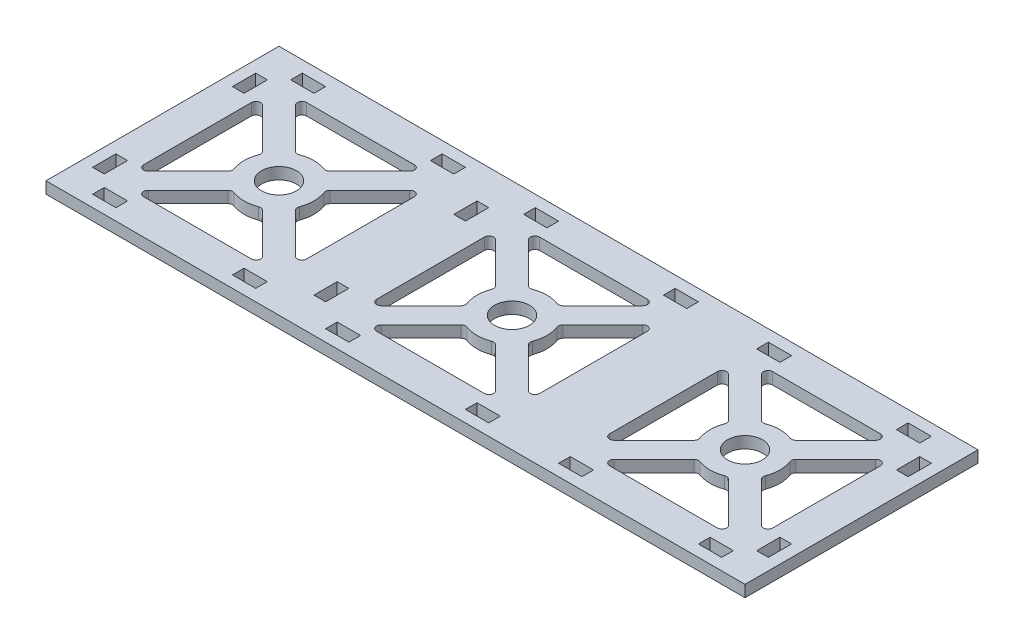
SolidWorks part; units mm, degrees
ref_plane "Front Plane" through (0, 0, 0) normal (0, 0, 1) x (1, 0, 0)
ref_plane "Top Plane" through (0, 0, 0) normal (0, 1, 0) x (1, 0, 0)
ref_plane "Right Plane" through (0, 0, 0) normal (1, 0, 0) x (0, 0, -1)
sketch "Sketch1" plane through (0, 0, 0) normal (0, 1, 0) x (1, 0, 0)
  line L0 (-966.8368, 0) -> (47375.0043, 0) construction
  line L1 (-23.1005, 35) -> (23.1005, 35)
  line L2 (-35, 23.1005) -> (-35, -23.1005)
  line L3 (-23.1005, -35) -> (23.1005, -35)
  line L4 (35, 23.1005) -> (35, -23.1005)
  line L5 (-35, 35) -> (35, -35) construction
  line L6 (-35, -35) -> (35, 35) construction
  line L7 (-50, 50) -> (150, 50)
  line L8 (-50, 50) -> (-50, -50) construction
  line L9 (-50, -50) -> (150, -50)
  line L10 (50, 50) -> (50, -50) construction
  line L11 (-50, 50) -> (50, -50) construction
  line L12 (-50, -50) -> (50, 50) construction
  line L13 (-31.5858, 24.5147) -> (-14.49, 7.4189)
  line L14 (-24.5147, 31.5858) -> (-7.4189, 14.49)
  line L15 (0, -1000) -> (0, 49000) construction
  line L16 (24.5147, 31.5858) -> (7.4189, 14.49)
  line L17 (31.5858, 24.5147) -> (14.49, 7.4189)
  line L18 (31.5858, -24.5147) -> (14.49, -7.4189)
  line L19 (24.5147, -31.5858) -> (7.4189, -14.49)
  line L20 (-24.5147, -31.5858) -> (-7.4189, -14.49)
  line L21 (-31.5858, -24.5147) -> (-14.49, -7.4189)
  line L22 (-35, 35) -> (-35, 27.9289) construction
  line L23 (-23.8844, 35) -> (-27.9289, 35) construction
  line L24 (27.9289, 35) -> (35, 35) construction
  line L25 (35, 35) -> (35, 27.9289) construction
  line L26 (35, -27.9289) -> (35, -35) construction
  line L27 (27.9289, -35) -> (35, -35) construction
  line L28 (-35, -35) -> (-27.9289, -35) construction
  line L29 (-35, -27.9289) -> (-35, -35) construction
  line L30 (135, -27.9289) -> (135, -35) construction
  line L31 (135, -35) -> (127.9289, -35) construction
  line L32 (72.0711, -35) -> (65, -35) construction
  line L33 (65, -27.9289) -> (65, -35) construction
  line L34 (65, 35) -> (65, 27.9289) construction
  line L35 (72.0711, 35) -> (65, 35) construction
  line L36 (123.8844, 35) -> (127.9289, 35) construction
  line L37 (135, 35) -> (135, 27.9289) construction
  line L38 (100, -1000) -> (100, 49000) construction
  line L39 (150, -50) -> (50, 50) construction
  line L40 (150, 50) -> (50, -50) construction
  line L41 (135, -35) -> (65, 35) construction
  line L42 (135, 35) -> (65, -35) construction
  line L43 (1066.8368, 0) -> (-47275.0043, 0) construction
  line L44 (131.5858, -24.5147) -> (114.49, -7.4189)
  line L45 (124.5147, -31.5858) -> (107.4189, -14.49)
  line L46 (75.4853, -31.5858) -> (92.5811, -14.49)
  line L47 (68.4142, -24.5147) -> (85.51, -7.4189)
  line L48 (68.4142, 24.5147) -> (85.51, 7.4189)
  line L49 (75.4853, 31.5858) -> (92.5811, 14.49)
  line L50 (124.5147, 31.5858) -> (107.4189, 14.49)
  line L51 (131.5858, 24.5147) -> (114.49, 7.4189)
  line L52 (150, 50) -> (150, -50)
  line L53 (65, 23.1005) -> (65, -23.1005)
  line L54 (123.1005, -35) -> (76.8995, -35)
  line L55 (135, 23.1005) -> (135, -23.1005)
  line L56 (123.1005, 35) -> (76.8995, 35)
  line L57 (-1166.8368, 0) -> (47175.0043, 0) construction
  line L58 (-65, -27.9289) -> (-65, -35) construction
  line L59 (-65, -35) -> (-72.0711, -35) construction
  line L60 (-127.9289, -35) -> (-135, -35) construction
  line L61 (-135, -27.9289) -> (-135, -35) construction
  line L62 (-135, 35) -> (-135, 27.9289) construction
  line L63 (-127.9289, 35) -> (-135, 35) construction
  line L64 (-76.1156, 35) -> (-72.0711, 35) construction
  line L65 (-65, 35) -> (-65, 27.9289) construction
  line L66 (-100, -1000) -> (-100, 49000) construction
  line L67 (-50, -50) -> (-150, 50) construction
  line L68 (-50, 50) -> (-150, -50) construction
  line L69 (-65, -35) -> (-135, 35) construction
  line L70 (-65, 35) -> (-135, -35) construction
  line L71 (866.8368, 0) -> (-47475.0043, 0) construction
  line L72 (-68.4142, -24.5147) -> (-85.51, -7.4189)
  line L73 (-75.4853, -31.5858) -> (-92.5811, -14.49)
  line L74 (-124.5147, -31.5858) -> (-107.4189, -14.49)
  line L75 (-131.5858, -24.5147) -> (-114.49, -7.4189)
  line L76 (-131.5858, 24.5147) -> (-114.49, 7.4189)
  line L77 (-124.5147, 31.5858) -> (-107.4189, 14.49)
  line L78 (-75.4853, 31.5858) -> (-92.5811, 14.49)
  line L79 (-68.4142, 24.5147) -> (-85.51, 7.4189)
  line L80 (-50, -50) -> (-150, -50)
  line L81 (-50, 50) -> (-150, 50)
  line L82 (-135, 23.1005) -> (-135, -23.1005)
  line L83 (-76.8995, -35) -> (-123.1005, -35)
  line L84 (-65, 23.1005) -> (-65, -23.1005)
  line L85 (-76.8995, 35) -> (-123.1005, 35)
  line L86 (-150, 50) -> (-150, -50)
  line L87 (-65, 40) -> (-75, 40)
  line L88 (-145, 45) -> (145, 45) construction
  line L89 (-145, 45) -> (-145, -45) construction
  line L90 (-145, -45) -> (145, -45) construction
  line L91 (145, 45) -> (145, -45) construction
  line L92 (-145, 45) -> (145, -45) construction
  line L93 (-145, -45) -> (145, 45) construction
  line L98 (-135, 45) -> (-125, 45)
  line L99 (-135, 45) -> (-135, 40)
  line L100 (-135, 40) -> (-125, 40)
  line L101 (-125, 45) -> (-125, 40)
  line L102 (-75, 45) -> (-75, 40)
  line L103 (-65, 45) -> (-75, 45)
  line L104 (-65, 45) -> (-65, 40)
  line L105 (-35, 45) -> (-35, 40)
  line L106 (-35, 40) -> (-25, 40)
  line L107 (-35, 45) -> (-25, 45)
  line L108 (-25, 45) -> (-25, 40)
  line L109 (125, 45) -> (125, 40)
  line L110 (135, 40) -> (125, 40)
  line L111 (135, 45) -> (135, 40)
  line L112 (135, 45) -> (125, 45)
  line L113 (25, 45) -> (25, 40)
  line L114 (35, 45) -> (25, 45)
  line L115 (35, 40) -> (25, 40)
  line L116 (35, 45) -> (35, 40)
  line L117 (65, 45) -> (65, 40)
  line L118 (65, 45) -> (75, 45)
  line L119 (75, 45) -> (75, 40)
  line L120 (65, 40) -> (75, 40)
  line L121 (135, -45) -> (125, -45)
  line L122 (135, -45) -> (135, -40)
  line L123 (135, -40) -> (125, -40)
  line L124 (125, -45) -> (125, -40)
  line L125 (65, -40) -> (75, -40)
  line L126 (75, -45) -> (75, -40)
  line L127 (65, -45) -> (75, -45)
  line L128 (65, -45) -> (65, -40)
  line L129 (35, -45) -> (35, -40)
  line L130 (35, -40) -> (25, -40)
  line L131 (35, -45) -> (25, -45)
  line L132 (25, -45) -> (25, -40)
  line L133 (-125, -45) -> (-125, -40)
  line L134 (-135, -40) -> (-125, -40)
  line L135 (-135, -45) -> (-135, -40)
  line L136 (-135, -45) -> (-125, -45)
  line L137 (-65, -45) -> (-65, -40)
  line L138 (-65, -45) -> (-75, -45)
  line L139 (-75, -45) -> (-75, -40)
  line L140 (-65, -40) -> (-75, -40)
  line L141 (-25, -45) -> (-25, -40)
  line L142 (-35, -45) -> (-25, -45)
  line L143 (-35, -40) -> (-25, -40)
  line L144 (-35, -45) -> (-35, -40)
  line L145 (-140, -35) -> (-140, -25)
  line L146 (-145, 35) -> (-140, 35)
  line L147 (-145, 35) -> (-145, 25)
  line L148 (-145, 25) -> (-140, 25)
  line L149 (-140, 35) -> (-140, 25)
  line L150 (-145, -25) -> (-140, -25)
  line L151 (-145, -35) -> (-145, -25)
  line L152 (-145, -35) -> (-140, -35)
  line L153 (145, -35) -> (140, -35)
  line L154 (145, -35) -> (145, -25)
  line L155 (145, -25) -> (140, -25)
  line L156 (140, -35) -> (140, -25)
  line L157 (140, 35) -> (140, 25)
  line L158 (145, 25) -> (140, 25)
  line L159 (145, 35) -> (145, 25)
  line L160 (145, 35) -> (140, 35)
  line L161 (-50, 35) -> (-50, 25)
  line L162 (-50, 35) -> (-45, 35)
  line L163 (-50, -35) -> (-45, -35)
  line L164 (-50, -25) -> (-45, -25)
  line L165 (-50, 25) -> (-45, 25)
  line L166 (-50, -35) -> (-50, -25)
  line L167 (-45, 35) -> (-45, 25)
  line L168 (-45, -35) -> (-45, -25)
  circle A0 centre (0, 0) radius 7.5
  arc A1 (-5.2983, -14.0331) -> (5.2983, -14.0331) centre (0, 0) ccw
  arc A2 (-13.5355, -6.4645) -> (-10.6066, -10.6066) centre (0, 0) ccw construction
  arc A3 (-10.6066, -10.6066) -> (-6.4645, -13.5355) centre (0, 0) ccw construction
  arc A4 (-10.6066, 10.6066) -> (-13.5355, 6.4645) centre (0, 0) ccw construction
  arc A5 (-14.0331, 5.2983) -> (-14.0331, -5.2983) centre (0, 0) ccw
  arc A6 (-6.4645, 13.5355) -> (-10.6066, 10.6066) centre (0, 0) ccw construction
  arc A7 (10.6066, 10.6066) -> (6.4645, 13.5355) centre (0, 0) ccw construction
  arc A8 (5.2983, 14.0331) -> (-5.2983, 14.0331) centre (0, 0) ccw
  arc A9 (13.5355, 6.4645) -> (10.6066, 10.6066) centre (0, 0) ccw construction
  arc A10 (10.6066, -10.6066) -> (13.5355, -6.4645) centre (0, 0) ccw construction
  arc A11 (14.0331, -5.2983) -> (14.0331, 5.2983) centre (0, 0) ccw
  arc A12 (6.4645, -13.5355) -> (10.6066, -10.6066) centre (0, 0) ccw construction
  arc A13 (-14.0331, 5.2983) -> (-14.49, 7.4189) centre (-15.9042, 6.0047) ccw
  arc A14 (-14.0331, -5.2983) -> (-14.49, -7.4189) centre (-15.9042, -6.0047) cw
  arc A15 (-31.5858, -24.5147) -> (-35, -23.1005) centre (-33, -23.1005) cw
  arc A16 (-31.5858, 24.5147) -> (-35, 23.1005) centre (-33, 23.1005) ccw
  arc A17 (-23.1005, -35) -> (-24.5147, -31.5858) centre (-23.1005, -33) cw
  arc A18 (23.1005, -35) -> (24.5147, -31.5858) centre (23.1005, -33) ccw
  arc A19 (7.4189, -14.49) -> (5.2983, -14.0331) centre (6.0047, -15.9042) ccw
  arc A20 (-5.2983, -14.0331) -> (-7.4189, -14.49) centre (-6.0047, -15.9042) ccw
  arc A21 (35, 23.1005) -> (31.5858, 24.5147) centre (33, 23.1005) ccw
  arc A22 (35, -23.1005) -> (31.5858, -24.5147) centre (33, -23.1005) cw
  arc A23 (14.49, -7.4189) -> (14.0331, -5.2983) centre (15.9042, -6.0047) cw
  arc A24 (14.0331, 5.2983) -> (14.49, 7.4189) centre (15.9042, 6.0047) cw
  arc A25 (7.4189, 14.49) -> (5.2983, 14.0331) centre (6.0047, 15.9042) cw
  arc A26 (-5.2983, 14.0331) -> (-7.4189, 14.49) centre (-6.0047, 15.9042) cw
  arc A27 (23.1005, 35) -> (24.5147, 31.5858) centre (23.1005, 33) cw
  arc A28 (-23.1005, 35) -> (-24.5147, 31.5858) centre (-23.1005, 33) ccw
  arc A29 (93.5355, -13.5355) -> (89.3934, -10.6066) centre (100, 0) cw construction
  arc A30 (89.3934, -10.6066) -> (86.4645, -6.4645) centre (100, 0) cw construction
  arc A31 (86.4645, 6.4645) -> (89.3934, 10.6066) centre (100, 0) cw construction
  arc A32 (89.3934, 10.6066) -> (93.5355, 13.5355) centre (100, 0) cw construction
  arc A33 (106.4645, 13.5355) -> (110.6066, 10.6066) centre (100, 0) cw construction
  arc A34 (110.6066, 10.6066) -> (113.5355, 6.4645) centre (100, 0) cw construction
  arc A35 (110.6066, -10.6066) -> (106.4645, -13.5355) centre (100, 0) cw construction
  arc A36 (113.5355, -6.4645) -> (110.6066, -10.6066) centre (100, 0) cw construction
  arc A37 (123.1005, 35) -> (124.5147, 31.5858) centre (123.1005, 33) cw
  arc A38 (76.8995, 35) -> (75.4853, 31.5858) centre (76.8995, 33) ccw
  arc A39 (105.2983, 14.0331) -> (107.4189, 14.49) centre (106.0047, 15.9042) ccw
  arc A40 (92.5811, 14.49) -> (94.7017, 14.0331) centre (93.9953, 15.9042) ccw
  arc A41 (85.9669, 5.2983) -> (85.51, 7.4189) centre (84.0958, 6.0047) ccw
  arc A42 (85.51, -7.4189) -> (85.9669, -5.2983) centre (84.0958, -6.0047) ccw
  arc A43 (65, -23.1005) -> (68.4142, -24.5147) centre (67, -23.1005) ccw
  arc A44 (65, 23.1005) -> (68.4142, 24.5147) centre (67, 23.1005) cw
  arc A45 (105.2983, -14.0331) -> (107.4189, -14.49) centre (106.0047, -15.9042) cw
  arc A46 (92.5811, -14.49) -> (94.7017, -14.0331) centre (93.9953, -15.9042) cw
  arc A47 (76.8995, -35) -> (75.4853, -31.5858) centre (76.8995, -33) cw
  arc A48 (123.1005, -35) -> (124.5147, -31.5858) centre (123.1005, -33) ccw
  arc A49 (131.5858, 24.5147) -> (135, 23.1005) centre (133, 23.1005) cw
  arc A50 (131.5858, -24.5147) -> (135, -23.1005) centre (133, -23.1005) ccw
  arc A51 (114.0331, -5.2983) -> (114.49, -7.4189) centre (115.9042, -6.0047) ccw
  arc A52 (114.0331, 5.2983) -> (114.49, 7.4189) centre (115.9042, 6.0047) cw
  arc A53 (85.9669, -5.2983) -> (85.9669, 5.2983) centre (100, 0) cw
  arc A54 (94.7017, 14.0331) -> (105.2983, 14.0331) centre (100, 0) cw
  arc A55 (114.0331, 5.2983) -> (114.0331, -5.2983) centre (100, 0) cw
  arc A56 (105.2983, -14.0331) -> (94.7017, -14.0331) centre (100, 0) cw
  circle A57 centre (100, 0) radius 7.5
  arc A58 (-106.4645, -13.5355) -> (-110.6066, -10.6066) centre (-100, 0) cw construction
  arc A59 (-110.6066, -10.6066) -> (-113.5355, -6.4645) centre (-100, 0) cw construction
  arc A60 (-113.5355, 6.4645) -> (-110.6066, 10.6066) centre (-100, 0) cw construction
  arc A61 (-110.6066, 10.6066) -> (-106.4645, 13.5355) centre (-100, 0) cw construction
  arc A62 (-93.5355, 13.5355) -> (-89.3934, 10.6066) centre (-100, 0) cw construction
  arc A63 (-89.3934, 10.6066) -> (-86.4645, 6.4645) centre (-100, 0) cw construction
  arc A64 (-89.3934, -10.6066) -> (-93.5355, -13.5355) centre (-100, 0) cw construction
  arc A65 (-86.4645, -6.4645) -> (-89.3934, -10.6066) centre (-100, 0) cw construction
  arc A66 (-76.8995, 35) -> (-75.4853, 31.5858) centre (-76.8995, 33) cw
  arc A67 (-123.1005, 35) -> (-124.5147, 31.5858) centre (-123.1005, 33) ccw
  arc A68 (-94.7017, 14.0331) -> (-92.5811, 14.49) centre (-93.9953, 15.9042) ccw
  arc A69 (-107.4189, 14.49) -> (-105.2983, 14.0331) centre (-106.0047, 15.9042) ccw
  arc A70 (-114.0331, 5.2983) -> (-114.49, 7.4189) centre (-115.9042, 6.0047) ccw
  arc A71 (-114.49, -7.4189) -> (-114.0331, -5.2983) centre (-115.9042, -6.0047) ccw
  arc A72 (-135, -23.1005) -> (-131.5858, -24.5147) centre (-133, -23.1005) ccw
  arc A73 (-135, 23.1005) -> (-131.5858, 24.5147) centre (-133, 23.1005) cw
  arc A74 (-94.7017, -14.0331) -> (-92.5811, -14.49) centre (-93.9953, -15.9042) cw
  arc A75 (-107.4189, -14.49) -> (-105.2983, -14.0331) centre (-106.0047, -15.9042) cw
  arc A76 (-123.1005, -35) -> (-124.5147, -31.5858) centre (-123.1005, -33) cw
  arc A77 (-76.8995, -35) -> (-75.4853, -31.5858) centre (-76.8995, -33) ccw
  arc A78 (-68.4142, 24.5147) -> (-65, 23.1005) centre (-67, 23.1005) cw
  arc A79 (-68.4142, -24.5147) -> (-65, -23.1005) centre (-67, -23.1005) ccw
  arc A80 (-85.9669, -5.2983) -> (-85.51, -7.4189) centre (-84.0958, -6.0047) ccw
  arc A81 (-85.9669, 5.2983) -> (-85.51, 7.4189) centre (-84.0958, 6.0047) cw
  arc A82 (-114.0331, -5.2983) -> (-114.0331, 5.2983) centre (-100, 0) cw
  arc A83 (-105.2983, 14.0331) -> (-94.7017, 14.0331) centre (-100, 0) cw
  arc A84 (-85.9669, 5.2983) -> (-85.9669, -5.2983) centre (-100, 0) cw
  arc A85 (-94.7017, -14.0331) -> (-105.2983, -14.0331) centre (-100, 0) cw
  circle A86 centre (-100, 0) radius 7.5
  dimension "D5" = 30
  dimension "D6" = 15
  dimension "D1" = 2
  dimension "D8" = 2
  dimension "1.5" = 15
  dimension "D2" = 15
  dimension "D3" = 100
  dimension "D4" = 100
  dimension "D7" = 5
  dimension "0.5" = 5
  dimension "D9" = 15
  dimension "D10" = 100
  dimension "D11" = 100
  dimension "D12" = 90
  dimension "D13" = 10
  dimension "D14" = 5
  dimension "D15" = 10
  dimension "D16" = 5
  dimension "D17" = 10
  dimension "D18" = 10
  dimension "D19" = 50
  dimension "D20" = 5
  dimension "D21" = 10
  dimension "D22" = 10
  dimension "D23" = 5
  dimension "D24" = 15
  dimension "D25" = 10
  dimension "D26" = 90
extrude "Boss-Extrude2" add sketch "Sketch1" along normal blind 5
